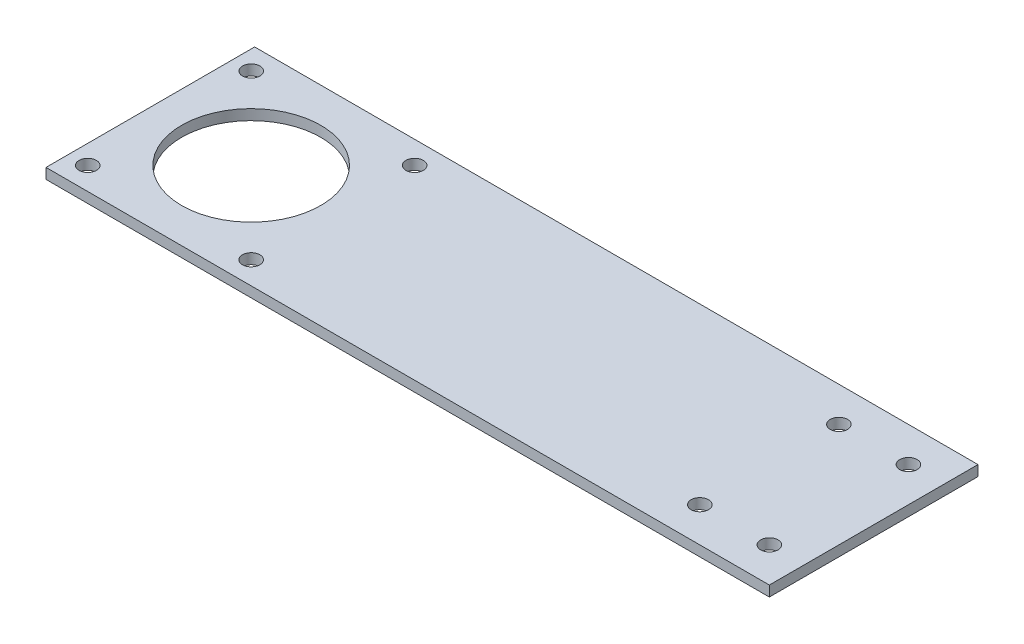
SolidWorks part; units mm, degrees
ref_plane "Front Plane" through (0, 0, 0) normal (0, 0, 1) x (1, 0, 0)
ref_plane "Top Plane" through (0, 0, 0) normal (0, 1, 0) x (1, 0, 0)
ref_plane "Right Plane" through (0, 0, 0) normal (1, 0, 0) x (0, 0, -1)
sketch "Sketch1" plane through (0, 0, 0) normal (0, 1, 0) x (1, 0, 0)
  line L0 (0, 0) -> (5.5, 0) construction
  line L1 (0, 0) -> (208, 0)
  line L2 (0, 0) -> (0, -60)
  line L3 (0, -60) -> (208, -60)
  line L4 (208, 0) -> (208, -60)
  line L5 (5.5, 0) -> (5.5, -6.5) construction
  line L6 (0, -30) -> (29, -30) construction
  line L7 (29, -30) -> (29, 0) construction
  line L8 (208, -60) -> (198, -60) construction
  line L9 (198, -60) -> (198, -50) construction
  line L10 (198, -50) -> (178, -50) construction
  line L11 (208, -30) -> (156.8395, -30) construction
  circle A0 centre (5.5, -6.5) radius 2.5
  circle A1 centre (52.5, -6.5) radius 2.5
  circle A2 centre (52.5, -53.5) radius 2.5
  circle A3 centre (5.5, -53.5) radius 2.5
  circle A4 centre (29, -30) radius 20
  circle A5 centre (178, -50) radius 2.5
  circle A6 centre (198, -50) radius 2.5
  circle A7 centre (178, -10) radius 2.5
  circle A8 centre (198, -10) radius 2.5
  dimension "D5" = 5
  dimension "D7" = 40
  dimension "D10" = 5
  dimension "D11" = 5
  dimension "D1" = 60
  dimension "D2" = 208
  dimension "D3" = 5.5
  dimension "D4" = 6.5
  dimension "D6" = 29
  dimension "D8" = 10
  dimension "D9" = 20
extrude "Boss-Extrude1" add sketch "Sketch1" along normal blind 3
